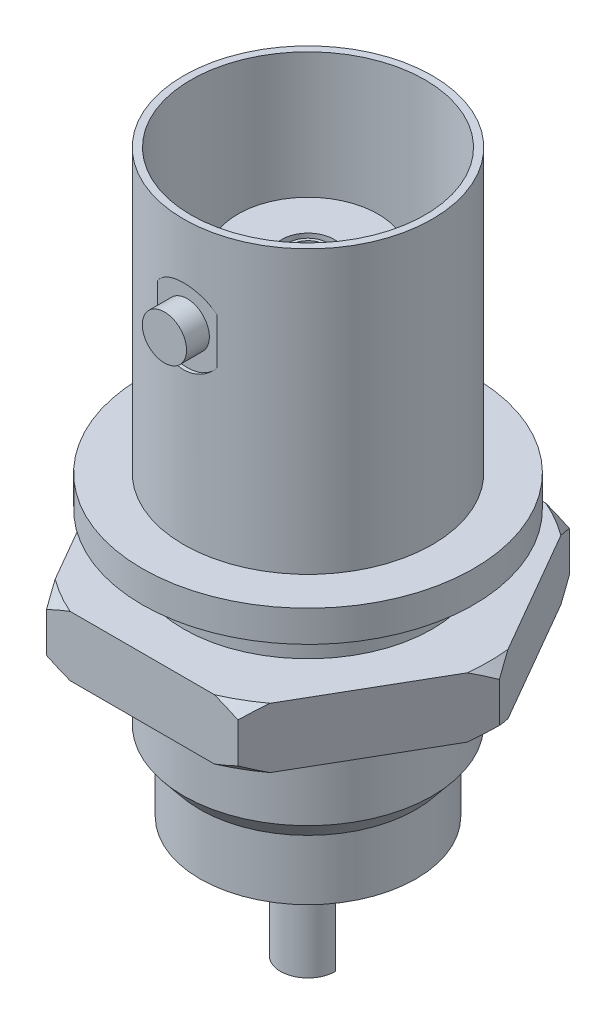
SolidWorks part; units mm, degrees
ref_plane "Front" through (0, 0, 0) normal (0, 0, 1) x (1, 0, 0)
ref_plane "Top" through (0, 0, 0) normal (0, 1, 0) x (1, 0, 0)
ref_plane "Right" through (0, 0, 0) normal (1, 0, 0) x (0, 0, -1)
sketch "Sketch1" plane through (0, 0, 0) normal (0, 0, 1) x (1, 0, 0)
  line L0 (0, 72.4023) -> (0, -72.4023) construction
  line L1 (-72.4023, 0) -> (72.4023, 0) construction
  line L2 (0, 7.2494) -> (-2.681, 7.2494)
  line L3 (-2.681, 7.2494) -> (-2.681, 0)
  line L4 (-2.681, 0) -> (-4.4849, 0)
  line L5 (-4.4849, 0) -> (-4.4849, 10.8)
  line L6 (-4.4849, 10.8) -> (-4.7625, 10.8)
  line L7 (-4.7625, 10.8) -> (-4.7625, 0)
  line L8 (-4.7625, 0) -> (-6.35, 0)
  line L9 (-6.35, 0) -> (-6.35, -1.2)
  line L10 (-6.35, -1.2) -> (-4.7625, -1.2)
  line L11 (-4.7625, -1.2) -> (-4.7625, -8.3368)
  line L12 (-4.7625, -8.3368) -> (-4.1387, -9.1)
  line L13 (-4.1387, -9.1) -> (-4.1387, -11.4)
  line L14 (-4.1387, -11.4) -> (-1.05, -11.4)
  line L15 (-1.05, -11.4) -> (-1.05, -13.0156)
  line L16 (-1.05, -13.0156) -> (0, -13.0156)
  line L17 (0, -13.0156) -> (0, 7.2494)
  dimension "D1" = 12.7
  dimension "D2" = 9.525
  dimension "D3" = 1.2
  dimension "D4" = 7.9
  dimension "D5" = 10.2
  dimension "D6" = 12
  dimension "D7" = 2.1
revolve "Revolve1" add sketch "Sketch1" angle 360 about L0
sketch "Sketch2" plane through (0, -1.2, 0) normal (0, -1, 0) x (1, 0, 0)
  line L1 (3.6662, -6.35) -> (7.3323, 0)
  line L2 (7.3323, 0) -> (3.6662, 6.35)
  line L3 (3.6662, 6.35) -> (-3.6662, 6.35)
  line L4 (-3.6662, 6.35) -> (-7.3323, 0)
  line L5 (-7.3323, 0) -> (-3.6662, -6.35)
  line L6 (-3.6662, -6.35) -> (3.6662, -6.35)
  circle A0 centre (0, 0) radius 6.35 construction
  circle A1 centre (0, 0) radius 4.7625 construction
  circle A2 centre (0, 0) radius 4.7625
  dimension "D1" = 12.7
extrude "Boss-Extrude1" add sketch "Sketch2" along normal blind 2.3 from offset 1.6
sketch "Sketch4" plane through (0, 0, 0) normal (0, 0, 1) x (1, 0, 0)
  line L0 (0, 10.8) -> (0, -12.3151) construction
  line L1 (4.7625, 10.8) -> (-4.7625, 10.8) construction
  line L2 (-7.3323, -3.95) -> (7.3323, -3.95) construction
  line L3 (-7.3323, -5.1) -> (-7.3323, -2.8) construction
  line L4 (7.3323, -5.1) -> (7.3323, -2.8) construction
  line L5 (-6.9256, -2.8) -> (-7.3323, -3.1865)
  line L6 (-3.6662, -2.8) -> (-7.3323, -2.8) construction
  line L7 (-7.3323, -3.1865) -> (-8.9993, -3.1865)
  line L8 (-8.9993, -3.1865) -> (-8.3611, -0.3273)
  line L9 (-8.3611, -0.3273) -> (-6.9256, 0.35)
  line L10 (-6.9256, 0.35) -> (-6.9256, -2.8)
  line L11 (-6.9256, -8.25) -> (-6.9256, -5.1)
  line L12 (-8.3611, -7.5727) -> (-6.9256, -8.25)
  line L13 (-8.9993, -4.7135) -> (-8.3611, -7.5727)
  line L14 (-7.3323, -4.7135) -> (-8.9993, -4.7135)
  line L15 (-6.9256, -5.1) -> (-7.3323, -4.7135)
revolve "Cut-Revolve1" cut sketch "Sketch4" angle 360 about L0
sketch "Sketch5" plane through (0, 0, 0) normal (0, 0, 1) x (1, 0, 0)
  line L0 (0, 12.1652) -> (0, 5.1451) construction
  circle A0 centre (0, 7.2451) radius 0.8469
extrude "Boss-Extrude2" add sketch "Sketch5" along normal blind 1 from offset 4.5
mirror "Mirror1" about plane through (0, 0, 0) normal (0, 0, 1) of "Boss-Extrude2"
sketch "Sketch6" plane through (0, 7.2494, 0) normal (0, 1, 0) x (1, 0, 0)
  circle A0 centre (0, 0) radius 0.6452
extrude "Cut-Extrude1" cut sketch "Sketch6" against normal blind 5
sketch "Sketch7" plane through (0, -13.0156, 0) normal (0, -1, 0) x (1, 0, 0)
  circle A0 centre (0, 0) radius 0.2
  dimension "D1" = 0.4
sketch "Sketch8" plane through (0, 0, 0) normal (-1, 0, 0) x (0, 0, 1)
  line L0 (0, -13.0156) -> (0, -13.7869)
  line L1 (-0.2, -13.0156) -> (0.2, -13.0156) construction
  line L2 (-0.3214, -14.8388) -> (-4.0876, -20.4277)
  arc A0 (0, -13.7869) -> (-0.3214, -14.8388) centre (-1.8823, -13.7869) cw
sweep "Sweep1" [suppressed] add profiles "Sketch7" path "Sketch8"
sketch "Sketch9" plane through (0, 0, 0) normal (1, 0, 0) x (0, 0, -1)
  line L0 (-5.5, 7.2451) -> (5.5, 7.2451) construction
  line L1 (-5.5, 8.0921) -> (-5.5, 6.3982) construction
  line L2 (5.5, 6.3982) -> (5.5, 8.0921) construction
  line L3 (0, 7.2451) -> (0, 10.6364) construction
  line L4 (4.7625, 8.0921) -> (4.6251, 8.0921)
  line L5 (4.7625, 8.0921) -> (4.7625, 8.6862)
  line L6 (4.7625, 8.6862) -> (4.6251, 8.6862)
  line L7 (4.6251, 8.0921) -> (4.6251, 8.6862)
  line L8 (-4.6251, 8.0921) -> (-4.6251, 8.6862)
  line L9 (-4.7625, 8.6862) -> (-4.6251, 8.6862)
  line L10 (-4.7625, 8.0921) -> (-4.7625, 8.6862)
  line L11 (-4.7625, 8.0921) -> (-4.6251, 8.0921)
revolve "Cut-Revolve2" cut sketch "Sketch9" angle 360 about L0
sketch "Sketch10" plane through (0, -13.0156, 0) normal (0, -1, 0) x (1, 0, 0)
  line L1 (0.944, 0) -> (1.05, 0)
  line L2 (-1.05, 0) -> (-0.944, 0)
  circle A0 centre (0, 0) radius 1.05 construction
  arc A1 (1.05, 0) -> (-1.05, 0) centre (0, 0) ccw
  arc A2 (0.944, 0) -> (-0.944, 0) centre (0, 0) ccw
extrude "Boss-Extrude3" add sketch "Sketch10" along normal blind 3
sketch "Sketch11" plane through (0, -13.0156, 0) normal (0, -1, 0) x (1, 0, 0)
  circle A0 centre (0, 0) radius 0.944
extrude "Cut-Extrude2" cut sketch "Sketch11" against normal blind 3
sketch "Sketch12" plane through (0, 0, 0) normal (1, 0, 0) x (0, 0, -1)
  line L2 (0, -16.0156) -> (0, -13.0156) construction
  line L3 (-1.05, -11.4) -> (-1.05, -16.0156) construction
  line L4 (0, -16.0156) -> (-0.6938, -16.4753)
  line L5 (-0.6938, -16.4753) -> (-1.7576, -16.2455)
  line L6 (-1.7576, -16.2455) -> (-1.7576, -16.1394)
  line L7 (-1.459, -15.197) -> (-1.05, -15.1084)
  line L9 (-1.459, -15.197) -> (-1.7576, -16.1394)
  arc A0 (0, -16.0156) -> (-1.05, -15.1084) centre (0, -14.9544) cw
extrude "Cut-Extrude3" [suppressed] cut sketch "Sketch12" against normal mid plane 13
sketch "Sketch13" plane through (0, 7.2494, 0) normal (0, 1, 0) x (1, 0, 0)
  circle A0 centre (0, 0) radius 0.7594
  circle A1 centre (0, 0) radius 0.9994
extrude "Cut-Extrude4" cut sketch "Sketch13" against normal blind 4
